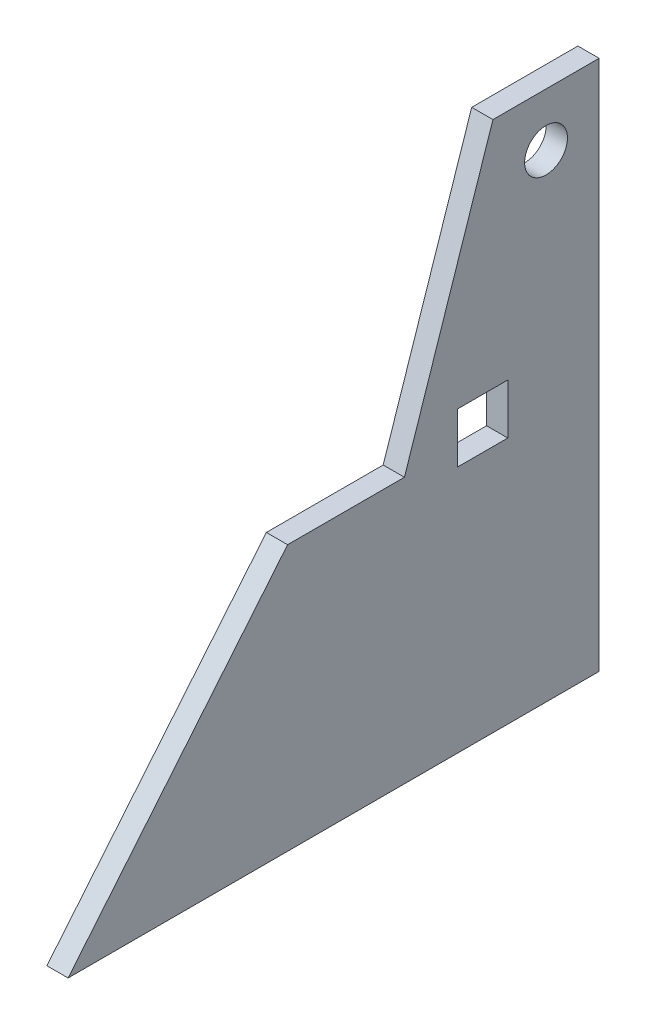
SolidWorks part; units mm, degrees
ref_plane "Front Plane" through (0, 0, 0) normal (0, 0, 1) x (1, 0, 0)
ref_plane "Top Plane" through (0, 0, 0) normal (0, 1, 0) x (1, 0, 0)
ref_plane "Right Plane" through (0, 0, 0) normal (1, 0, 0) x (0, 0, -1)
sketch "Sketch1" plane through (0, 0, 0) normal (1, 0, 0) x (0, 0, -1)
  line L0 (-150, 0) -> (-88, 75)
  line L1 (-150, 0) -> (0, 0)
  line L3 (-30, 150) -> (0, 150)
  line L4 (0, 0) -> (0, 150)
  line L5 (-30, 150) -> (-55, 75)
  line L6 (-25.8, 70) -> (-40, 70)
  line L7 (-25.8, 70) -> (-25.8, 84.2)
  line L8 (-25.8, 84.2) -> (-40, 84.2)
  line L9 (-40, 70) -> (-40, 84.2)
  line L10 (-25.8, 70) -> (-40, 84.2) construction
  line L11 (-25.8, 84.2) -> (-40, 70) construction
  line L12 (-55, 75) -> (-88, 75)
  circle A0 centre (-15, 135) radius 6.05
  point P0 (0, 0)
  point P3 (-32.9, 77.1)
  point P13 (-88.3632, 75)
  point P16 (-111.3142, 75)
  dimension "D4" = 12.1
  dimension "D1" = 150
  dimension "D2" = 150
  dimension "D3" = 30
  dimension "D5" = 15
  dimension "D6" = 15
  dimension "D7" = 70
  dimension "D8" = 40
  dimension "D9" = 14.2
  dimension "D10" = 14.2
  dimension "D11" = 75
  dimension "D12" = 15
  dimension "D13" = 33
extrude "Boss-Extrude1" add sketch "Sketch1" along normal blind 6
